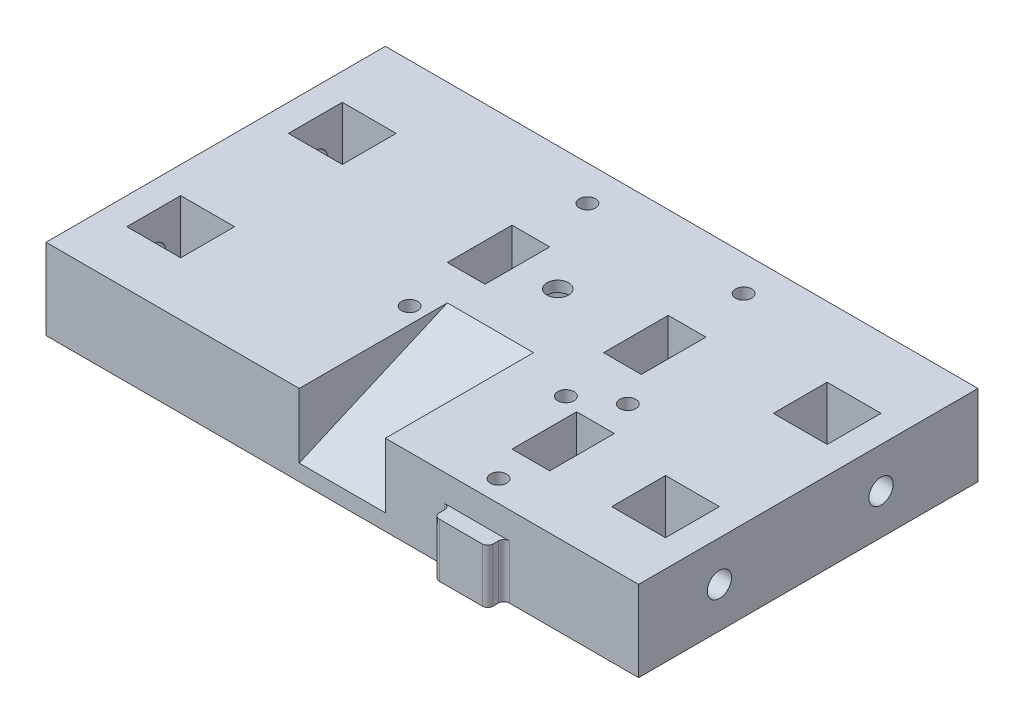
SolidWorks part; units mm, degrees
ref_plane "Alzado" through (0, 0, 0) normal (0, 0, 1) x (1, 0, 0)
ref_plane "Planta" through (0, 0, 0) normal (0, 1, 0) x (1, 0, 0)
ref_plane "Vista lateral" through (0, 0, 0) normal (1, 0, 0) x (0, 0, -1)
sketch "Croquis1" plane through (0, 0, 0) normal (0, 1, 0) x (1, 0, 0)
  line L0 (-50, 0) -> (55, 0) construction
  line L1 (0, 7.5) -> (-6.4952, 3.75)
  line L2 (-6.4952, 3.75) -> (-6.4952, -3.75)
  line L3 (-6.4952, -3.75) -> (0, -7.5)
  line L4 (0, -7.5) -> (6.4952, -3.75)
  line L5 (6.4952, -3.75) -> (6.4952, 3.75)
  line L6 (6.4952, 3.75) -> (0, 7.5)
  line L7 (-50, 20) -> (50, 20) construction
  line L8 (-50, -40) -> (50, -40) construction
  line L9 (-50, 10) -> (50, 10) construction
  line L10 (-50, 20) -> (-40, 20)
  line L11 (-50, 20) -> (-50, -40)
  line L12 (-50, -40) -> (-40, -40)
  line L13 (-40, 20) -> (-40, -40)
  line L14 (50, 20) -> (40, 20)
  line L15 (50, 20) -> (50, -40)
  line L16 (50, -40) -> (40, -40)
  line L17 (40, 20) -> (40, -40)
  line L18 (-40, 20) -> (40, 20)
  line L19 (-40, 20) -> (-40, -40)
  line L20 (-40, -40) -> (40, -40)
  line L21 (40, 20) -> (40, -40)
  line L22 (-50, -20) -> (50, -20) construction
  line L23 (-50, -30) -> (50, -30) construction
  line L24 (-14.5, 12.5) -> (21.5, 12.5) construction
  line L25 (-50, 10) -> (-40, 10)
  line L26 (-50, 10) -> (-50, 0)
  line L27 (-50, 0) -> (-40, 0)
  line L28 (-40, 10) -> (-40, 0)
  line L29 (50, 10) -> (40, 10)
  line L30 (50, 10) -> (50, 0)
  line L31 (50, 0) -> (40, 0)
  line L32 (40, 10) -> (40, 0)
  line L33 (50, -20) -> (40, -20)
  line L34 (50, -20) -> (50, -30)
  line L35 (50, -30) -> (40, -30)
  line L36 (40, -20) -> (40, -30)
  line L37 (-50, -20) -> (-40, -20)
  line L38 (-50, -20) -> (-50, -30)
  line L39 (-50, -30) -> (-40, -30)
  line L40 (-40, -20) -> (-40, -30)
  line L41 (-50, 20) -> (-55, 20)
  line L42 (-50, 20) -> (-50, -40)
  line L43 (-50, -40) -> (-55, -40)
  line L44 (-55, 20) -> (-55, -40)
  line L45 (50, 20) -> (55, 20)
  line L46 (50, 20) -> (50, -40)
  line L47 (50, -40) -> (55, -40)
  line L48 (55, 20) -> (55, -40)
  line L49 (-14.5, -12.5) -> (21.5, -12.5) construction
  line L50 (-11, 12.5) -> (-11, -12.5) construction
  line L51 (-14.5, 12.5) -> (-7.5, 12.5)
  line L52 (-14.5, 12.5) -> (-14.5, -12.5)
  line L53 (-14.5, -12.5) -> (-7.5, -12.5)
  line L54 (-7.5, 12.5) -> (-7.5, -12.5)
  line L55 (21.5, 12.5) -> (14.5, 12.5)
  line L56 (21.5, 12.5) -> (21.5, -12.5)
  line L57 (21.5, -12.5) -> (14.5, -12.5)
  line L58 (14.5, 12.5) -> (14.5, -12.5)
  line L59 (-14.5, 6) -> (-7.5, 6)
  line L60 (-14.5, 6) -> (-14.5, -6)
  line L61 (-14.5, -6) -> (-7.5, -6)
  line L62 (-7.5, 6) -> (-7.5, -6)
  line L63 (14.5, 6) -> (21.5, 6)
  line L64 (14.5, 6) -> (14.5, -6)
  line L65 (14.5, -6) -> (21.5, -6)
  line L66 (21.5, 6) -> (21.5, -6)
  line L67 (18, 12.5) -> (18, -12.5) construction
  circle A0 centre (0, 0) radius 7.5 construction
  circle A1 centre (-11, 16.5) radius 1.5
  circle A2 centre (18, 16.5) radius 1.5
  circle A3 centre (-11, -16.5) radius 1.5
  circle A4 centre (18, -16.5) radius 1.5
  dimension "D1" = 15
  dimension "D24" = 3
  dimension "D25" = 3
  dimension "D26" = 3
  dimension "D27" = 3
  dimension "D2" = 100
  dimension "D3" = 10
  dimension "D4" = 10
  dimension "D5" = 20
  dimension "D6" = 50
  dimension "D7" = 60
  dimension "D8" = 10
  dimension "D9" = 20
  dimension "D10" = 10
  dimension "D11" = 5
  dimension "D12" = 5
  dimension "D13" = 40
  dimension "D14" = 7
  dimension "D15" = 7
  dimension "D16" = 25
  dimension "D17" = 12.5
  dimension "D18" = 7.5
  dimension "D19" = 14.5
  dimension "D20" = 12
  dimension "D21" = 12
  dimension "D22" = 6.5
  dimension "D23" = 6.5
  dimension "D28" = 4
  dimension "D29" = 4
  dimension "D30" = 4
  dimension "D31" = 4
  dimension "D32" = 3.5
  dimension "D33" = 3.5
  dimension "D34" = 3.5
  dimension "D35" = 3.5
extrude "Saliente-Extruir1" add sketch "Croquis1" along normal blind 15 contours L13 L19 L20 L17 L21 L18 A4 A3 A2 A1 L58 L55 L56 L57 L6 L5 L4 L3 L2 L1 L51 L54 L53 L52 | L11 L37 L13 L27 | L39 L11 L12 L13 | L41 L44 L43 L11 | L11 L25 L13 L10 | L29 L15 L14 L17 | L48 L45 L15 L47 | L33 L15 L31 L17 | L15 L35 L17 L16 | L52 L59 L54 L51 | L61 L52 L53 L54 | L58 L63 L56 L55 | L65 L58 L57 L56
sketch "Croquis2" plane through (0, 0, 0) normal (0, -1, 0) x (1, 0, 0)
  line L1 (-6.9585, 16.5) -> (-8.9793, 20)
  line L2 (-8.9793, 20) -> (-13.0207, 20)
  line L3 (-13.0207, 20) -> (-15.0415, 16.5)
  line L4 (-15.0415, 16.5) -> (-13.0207, 13)
  line L5 (-13.0207, 13) -> (-8.9793, 13)
  line L6 (-8.9793, 13) -> (-6.9585, 16.5)
  line L7 (22.0415, 16.5) -> (20.0207, 20)
  line L8 (20.0207, 20) -> (15.9793, 20)
  line L9 (15.9793, 20) -> (13.9585, 16.5)
  line L10 (13.9585, 16.5) -> (15.9793, 13)
  line L11 (15.9793, 13) -> (20.0207, 13)
  line L12 (20.0207, 13) -> (22.0415, 16.5)
  line L13 (-6.9585, -16.5) -> (-8.9793, -13)
  line L14 (-8.9793, -13) -> (-13.0207, -13)
  line L15 (-13.0207, -13) -> (-15.0415, -16.5)
  line L16 (-15.0415, -16.5) -> (-13.0207, -20)
  line L17 (-13.0207, -20) -> (-8.9793, -20)
  line L18 (-8.9793, -20) -> (-6.9585, -16.5)
  line L19 (22.0415, -16.5) -> (20.0207, -13)
  line L20 (20.0207, -13) -> (15.9793, -13)
  line L21 (15.9793, -13) -> (13.9585, -16.5)
  line L22 (13.9585, -16.5) -> (15.9793, -20)
  line L23 (15.9793, -20) -> (20.0207, -20)
  line L24 (20.0207, -20) -> (22.0415, -16.5)
  circle A0 centre (-11, 16.5) radius 3.5 construction
  circle A1 centre (18, 16.5) radius 3.5 construction
  circle A2 centre (-11, -16.5) radius 3.5 construction
  circle A3 centre (18, -16.5) radius 3.5 construction
  dimension "D1" = 7
  dimension "D2" = 7
  dimension "D3" = 7
  dimension "D4" = 7
extrude "Cortar-Extruir1" cut sketch "Croquis2" against normal blind 5
sketch "Croquis3" plane through (55, 0, 0) normal (1, 0, 0) x (0, 0, -1)
  line L0 (-40, 7.5) -> (20, 7.5) construction
  line L1 (-40, 15) -> (-40, 0) construction
  line L2 (20, 15) -> (20, 0) construction
  circle A0 centre (-25, 7.5) radius 1.5
  circle A1 centre (5, 7.5) radius 1.5
  dimension "D3" = 3
  dimension "D4" = 3
  dimension "D1" = 15
  dimension "D2" = 15
extrude "Cortar-Extruir2" cut sketch "Croquis3" against normal blind 25
sketch "Croquis6" plane through (-55, 0, 0) normal (-1, 0, 0) x (0, 0, 1)
  line L0 (-20, 7.5) -> (40, 7.5) construction
  line L1 (-20, 15) -> (-20, 0) construction
  line L2 (40, 15) -> (40, 0) construction
  circle A0 centre (-5, 7.5) radius 1.5
  circle A1 centre (25, 7.5) radius 1.5
  dimension "D1" = 3
  dimension "D2" = 3
  dimension "D3" = 15
  dimension "D4" = 15
extrude "Cortar-Extruir3" cut sketch "Croquis6" against normal blind 25
sketch "Croquis8" plane through (0, 15, 0) normal (0, 1, 0) x (1, 0, 0)
  line L0 (-7.5, 6) -> (-7.5, -6) construction
  line L1 (7.5, -8.9193) -> (-7.5, -8.9193)
  line L2 (7.5, -8.9193) -> (7.5, 8.9193)
  line L3 (7.5, 8.9193) -> (-7.5, 8.9193)
  line L4 (-7.5, -8.9193) -> (-7.5, 8.9193)
  line L5 (7.5, -8.9193) -> (-7.5, 8.9193) construction
  line L6 (7.5, 8.9193) -> (-7.5, -8.9193) construction
  circle A0 centre (0, 0) radius 2
  point P0 (0, 0)
  dimension "D1" = 4
extrude "Saliente-Extruir2" add sketch "Croquis8" against normal blind 2
sketch "Croquis9" plane through (55, 0, 0) normal (1, 0, 0) x (0, 0, -1)
  line L0 (-12.5, 15) -> (-40, 3)
  line L1 (-40, 15) -> (0, 15)
  line L2 (-40, 15) -> (-40, 0)
  line L3 (-40, 0) -> (0, 0)
  line L4 (0, 15) -> (0, 0)
  circle M5 centre (-25, 7.5) radius 1.5
  line M7 (-40, 0) -> (20, 0)
  line M9 (20, 15) -> (-40, 15)
  line M10 (-40, 15) -> (-40, 0)
  dimension "D1" = 12.5
  dimension "D2" = 3
extrude "Cortar-Extruir4" cut sketch "Croquis9" against normal mid plane 16 from offset 55 contours L4 L0 M9 M10 M7 M5 offset against normal yes
sketch "Croquis10" plane through (0, 15, 0) normal (0, 1, 0) x (1, 0, 0)
  line L0 (25, 20) -> (25, -40) construction
  line L1 (-55, 20) -> (55, 20) construction
  line L2 (8, -40) -> (55, -40) construction
  line L4 (21.5, -30) -> (28.5, -30)
  line L5 (21.5, -30) -> (21.5, -18)
  line L6 (21.5, -18) -> (28.5, -18)
  line L7 (28.5, -30) -> (28.5, -18)
  line L8 (21.5, -30) -> (28.5, -18) construction
  line L9 (21.5, -18) -> (28.5, -30) construction
  circle A0 centre (25, -12) radius 1.5
  circle A1 centre (25, -36) radius 1.5
  point P6 (25, -24)
  dimension "D5" = 3
  dimension "D6" = 3
  dimension "D1" = 25
  dimension "D2" = 7
  dimension "D3" = 12
  dimension "D4" = 24
  dimension "D7" = 6
  dimension "D8" = 6
extrude "Cortar-Extruir5" cut sketch "Croquis10" against normal blind 16
sketch "Croquis12" plane through (0, 0, -20) normal (0, 0, -1) x (-1, 0, 0)
  line L1 (-55, 15) -> (55, 15)
  line L2 (-55, 15) -> (-55, 0)
  line L3 (-55, 0) -> (55, 0)
  line L4 (55, 15) -> (55, 0)
extrude "Saliente-Extruir3" add sketch "Croquis12" along normal blind 3
sketch "Croquis13" plane through (0, 0, 0) normal (0, -1, 0) x (1, 0, 0)
  line L1 (29.0415, 12) -> (27.0207, 15.5)
  line L2 (27.0207, 15.5) -> (22.9793, 15.5)
  line L3 (22.9793, 15.5) -> (20.9585, 12)
  line L4 (20.9585, 12) -> (22.9793, 8.5)
  line L5 (22.9793, 8.5) -> (27.0207, 8.5)
  line L6 (27.0207, 8.5) -> (29.0415, 12)
  line L7 (29.0415, 36) -> (27.0207, 39.5)
  line L8 (27.0207, 39.5) -> (22.9793, 39.5)
  line L9 (22.9793, 39.5) -> (20.9585, 36)
  line L10 (20.9585, 36) -> (22.9793, 32.5)
  line L11 (22.9793, 32.5) -> (27.0207, 32.5)
  line L12 (27.0207, 32.5) -> (29.0415, 36)
  circle A0 centre (25, 12) radius 3.5 construction
  circle A1 centre (25, 36) radius 3.5 construction
  dimension "D1" = 7
  dimension "D2" = 7
extrude "Cortar-Extruir6" cut sketch "Croquis13" against normal blind 5
sketch "Croquis14" plane through (0, 0, 0) normal (0, -1, 0) x (1, 0, 0)
  line L0 (-55, 40) -> (55, 40) construction
  line L2 (30, 41) -> (30, 42)
  line L3 (29, 43) -> (21, 43)
  line L4 (20, 41) -> (20, 42)
  line L5 (19, 40) -> (31, 40)
  circle A0 centre (25, 36) radius 1.5 construction
  arc A1 (30, 42) -> (29, 43) centre (29, 42) ccw
  arc A2 (21, 43) -> (20, 42) centre (21, 42) ccw
  arc A3 (20, 41) -> (19, 40) centre (19, 41) cw
  arc A4 (31, 40) -> (30, 41) centre (31, 41) cw
  dimension "D4" = 1
  dimension "D5" = 1
  dimension "D1" = 3
  dimension "D2" = 5
  dimension "D3" = 5
extrude "Saliente-Extruir4" add sketch "Croquis14" against normal blind 10
sketch "Croquis15" plane through (55, 0, 0) normal (1, 0, 0) x (0, 0, -1)
  circle A0 centre (-25, 7.5) radius 2.25
  circle A1 centre (5, 7.5) radius 2.25
  dimension "D1" = 4.5
  dimension "D2" = 4.5
extrude "Cortar-Extruir7" cut sketch "Croquis15" against normal blind 10
sketch "Croquis16" plane through (-55, 0, 0) normal (-1, 0, 0) x (0, 0, 1)
  circle A0 centre (-5, 7.5) radius 2.25
  circle A1 centre (25, 7.5) radius 2.25
  dimension "D1" = 4.5
  dimension "D2" = 4.5
extrude "Cortar-Extruir8" cut sketch "Croquis16" against normal blind 10
